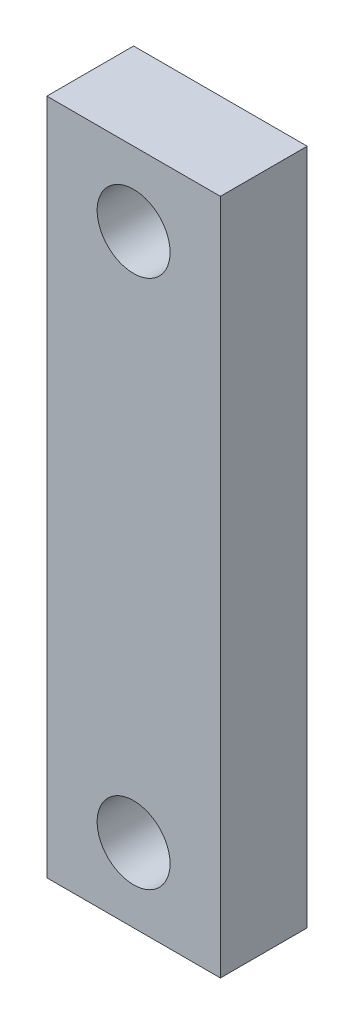
SolidWorks part; units mm, degrees
ref_plane "Front Plane" through (0, 0, 0) normal (0, 0, 1) x (1, 0, 0)
ref_plane "Top Plane" through (0, 0, 0) normal (0, 1, 0) x (1, 0, 0)
ref_plane "Right Plane" through (0, 0, 0) normal (1, 0, 0) x (0, 0, -1)
sketch "Sketch1" plane through (0, 0, 0) normal (0, 0, 1) x (1, 0, 0)
  line L1 (10, 39) -> (-10, 39)
  line L2 (10, 39) -> (10, -39)
  line L3 (10, -39) -> (-10, -39)
  line L4 (-10, 39) -> (-10, -39)
  line L5 (10, 39) -> (-10, -39) construction
  line L6 (10, -39) -> (-10, 39) construction
  point P0 (0, 0)
  point P5 (0, 0)
  dimension "D1" = 20
  dimension "D2" = 78
extrude "Boss-Extrude1" add sketch "Sketch1" along normal blind 10
hole_wizard "M8 Clearance Hole1" positions "Sketch2" profile "Sketch3" hole size "M8" standard "ISO" end condition through all
sketch "Sketch2" plane through (0, 0, 10) normal (0, 0, 1) x (1, 0, 0)
  line L0 (10, 39) -> (-10, 39) construction
  line L1 (-10, -39) -> (10, -39) construction
  point P0 (0, 30.5)
  point P2 (0, -30.5)
  dimension "D1" = 8.5
  dimension "D2" = 8.5
sketch "Sketch3" plane through (0, 30.5, 10) normal (1, 0, 0) x (0, -1, 0)
  line L0 (0, 0) -> (0, 10)
  line L1 (0, 10) -> (4.2, 10)
  line L2 (4.2, 10) -> (4.2, 0)
  line L5 (4.2, 0) -> (0, 0)
  line L11 (0, -6.35) -> (0, 107.95) construction
  dimension "Thru Hole Dia." = 8.4
  dimension "Thru Hole Depth" = 10
